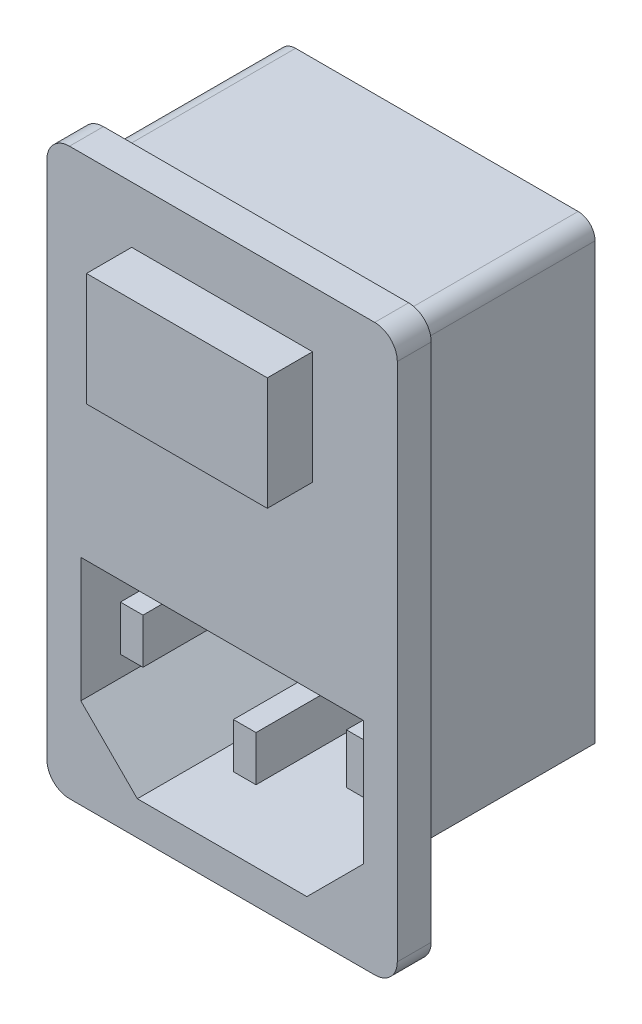
SolidWorks part; units mm, degrees
ref_plane "Front Plane" through (0, 0, 0) normal (0, 0, 1) x (1, 0, 0)
ref_plane "Top Plane" through (0, 0, 0) normal (0, 1, 0) x (1, 0, 0)
ref_plane "Right Plane" through (0, 0, 0) normal (1, 0, 0) x (0, 0, -1)
sketch "Sketch1" plane through (0, 0, 0) normal (0, 0, 1) x (1, 0, 0)
  line L1 (-13.5, 25) -> (13.5, 25)
  line L2 (-15.5, 23) -> (-15.5, -23)
  line L3 (-13.5, -25) -> (13.5, -25)
  line L4 (15.5, 23) -> (15.5, -23)
  line L5 (0, -25) -> (0, 25) construction
  line L6 (-15.5, 0) -> (15.5, 0) construction
  arc A0 (13.5, -25) -> (15.5, -23) centre (13.5, -23) ccw
  arc A1 (-15.5, -23) -> (-13.5, -25) centre (-13.5, -23) ccw
  arc A2 (13.5, 25) -> (15.5, 23) centre (13.5, 23) cw
  arc A3 (-13.5, 25) -> (-15.5, 23) centre (-13.5, 23) ccw
  point P0 (0, 0)
  point P8 (-15.5, -25)
  point P11 (15.5, 25)
  point P15 (-15.5, 25)
  dimension "D3" = 2
  dimension "D1" = 31
  dimension "D2" = 50
extrude "Boss-Extrude1" add sketch "Sketch1" along normal blind 3
sketch "Sketch2" plane through (0, 0, 0) normal (0, 0, -1) x (-1, 0, 0)
  line L0 (0, 25) -> (0, -25) construction
  line L1 (-13.5, 25) -> (13.5, 25) construction
  line L2 (13.5, -25) -> (-13.5, -25) construction
  line L3 (5.1244, -23.5) -> (5.1244, -16.5) construction
  line L4 (-12.5, 23.5) -> (12.5, 23.5)
  line L5 (-14, 22) -> (-14, -16.5)
  line L6 (-7, -23.5) -> (7, -23.5)
  line L7 (14, 22) -> (14, -16.5)
  line L8 (0, -23.5) -> (0, 23.5) construction
  line L9 (-14, 0) -> (14, 0) construction
  line L10 (-18.7646, -16.5) -> (25.0539, -16.5) construction
  line L11 (-14, -16.5) -> (-7, -23.5)
  line L12 (7, -23.5) -> (14, -16.5)
  arc A0 (12.5, 23.5) -> (14, 22) centre (12.5, 22) cw
  arc A1 (-12.5, 23.5) -> (-14, 22) centre (-12.5, 22) ccw
  point P6 (0, 0)
  point P7 (14, -23.5)
  point P9 (-14, -23.5)
  point P20 (14, 23.5)
  point P24 (-14, 23.5)
  dimension "D4" = 1.5
  dimension "D1" = 47
  dimension "D2" = 28
  dimension "D3" = 7
extrude "Boss-Extrude2" add sketch "Sketch2" along normal blind 16
sketch "Sketch3" plane through (0, 0, 3) normal (0, 0, 1) x (1, 0, 0)
  line L0 (0, 25) -> (0, 15) construction
  line L1 (13.5, 25) -> (-13.5, 25) construction
  line L3 (-8, 20) -> (8, 20)
  line L4 (-8, 20) -> (-8, 10)
  line L5 (-8, 10) -> (8, 10)
  line L6 (8, 20) -> (8, 10)
  line L7 (0, 10) -> (0, 20) construction
  line L8 (-8, 15) -> (8, 15) construction
  dimension "D1" = 10
  dimension "D2" = 10
  dimension "D3" = 16
extrude "Boss-Extrude3" add sketch "Sketch3" along normal blind 4
sketch "Sketch4" plane through (0, 0, 3) normal (0, 0, 1) x (1, 0, 0)
  line L0 (0, -25) -> (0, -14) construction
  line L1 (-13.5, -25) -> (13.5, -25) construction
  line L2 (-12.5, -17) -> (-7.5, -22)
  line L3 (-12.5, -6) -> (12.5, -6)
  line L4 (-12.5, -6) -> (-12.5, -17)
  line L5 (-7.5, -22) -> (7.5, -22)
  line L6 (12.5, -6) -> (12.5, -17)
  line L7 (0, -22) -> (0, -6) construction
  line L8 (-12.5, -14) -> (12.5, -14) construction
  line L9 (7.5, -22) -> (12.5, -17)
  point P5 (12.5, -22)
  point P7 (-12.5, -22)
  dimension "D1" = 11
  dimension "D2" = 16
  dimension "D3" = 25
extrude "Cut-Extrude1" cut sketch "Sketch4" against normal blind 17
sketch "Sketch5" plane through (0, 0, -14) normal (0, 0, 1) x (1, 0, 0)
  line L0 (0, -6) -> (0, -22) construction
  line L1 (12.5, -6) -> (-12.5, -6) construction
  line L2 (-7.5, -22) -> (7.5, -22) construction
  line L3 (-1, -13.6805) -> (-10, -13.6805) construction
  line L4 (-1, -13.6805) -> (1, -13.6805)
  line L5 (-1, -13.6805) -> (-1, -17.6805)
  line L6 (-1, -17.6805) -> (1, -17.6805)
  line L7 (1, -13.6805) -> (1, -17.6805)
  line L8 (0, -17.6805) -> (0, -13.6805) construction
  line L9 (-1, -15.6805) -> (1, -15.6805) construction
  line L10 (-10, -13.6805) -> (-10, -11.6805) construction
  line L11 (1, -13.6805) -> (10, -13.6805) construction
  line L12 (-11, -9.6805) -> (-9, -9.6805)
  line L13 (-11, -9.6805) -> (-11, -13.6805)
  line L14 (-11, -13.6805) -> (-9, -13.6805)
  line L15 (-9, -9.6805) -> (-9, -13.6805)
  line L16 (-10, -13.6805) -> (-10, -9.6805) construction
  line L17 (-11, -11.6805) -> (-9, -11.6805) construction
  line L18 (10, -13.6805) -> (10, -11.6805) construction
  line L20 (9, -9.4692) -> (11, -9.4692)
  line L21 (9, -9.4692) -> (9, -13.8919)
  line L22 (9, -13.8919) -> (11, -13.8919)
  line L23 (11, -9.4692) -> (11, -13.8919)
  line L24 (10, -13.8919) -> (10, -9.4692) construction
  line L25 (9, -11.6805) -> (11, -11.6805) construction
  point P6 (0, -15.6805)
  dimension "D1" = 4
  dimension "D2" = 9
  dimension "D3" = 2
  dimension "D4" = 2
  dimension "D5" = 2
  dimension "D6" = 9
  dimension "D7" = 2
  dimension "D8" = 2
extrude "Boss-Extrude4" add sketch "Sketch5" along normal blind 15
